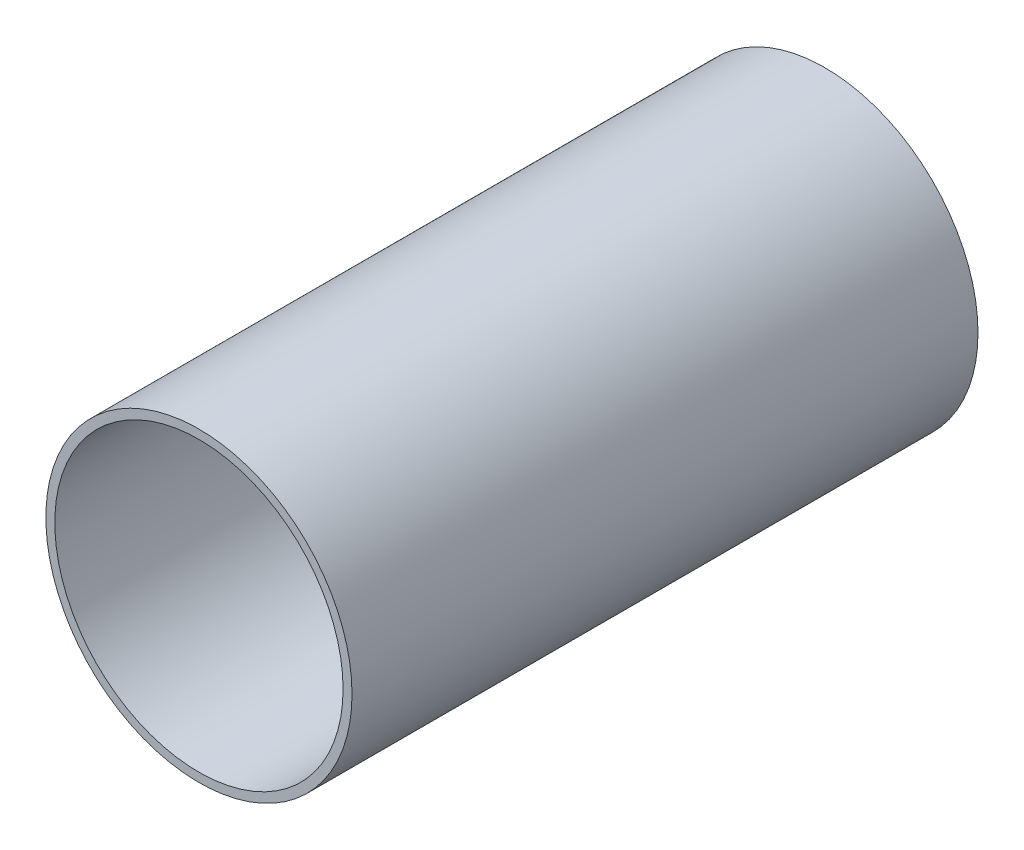
SolidWorks part; units mm, degrees
material "Plain Carbon Steel"
ref_plane "Front Plane" through (0, 0, 0) normal (0, 0, 1) x (1, 0, 0)
ref_plane "Top Plane" through (0, 0, 0) normal (0, 1, 0) x (1, 0, 0)
ref_plane "Right Plane" through (0, 0, 0) normal (1, 0, 0) x (0, 0, -1)
sketch "Sketch4" plane through (0, 0, 0) normal (0, 0, 1) x (1, 0, 0)
  circle A1 centre (12409.7404, 3023.0315) radius 161.1865
extrude "Extrude-Thin1" add sketch "Sketch4" along normal blind 700 thin
sketch "Sketch5" plane through (0, 0, 0) normal (0, 0, 1) x (1, 0, 0)
  circle A0 centre (12409.7404, 3023.0315) radius 171.1865
extrude "Boss-Extrude1" add sketch "Sketch5" along normal blind 10
